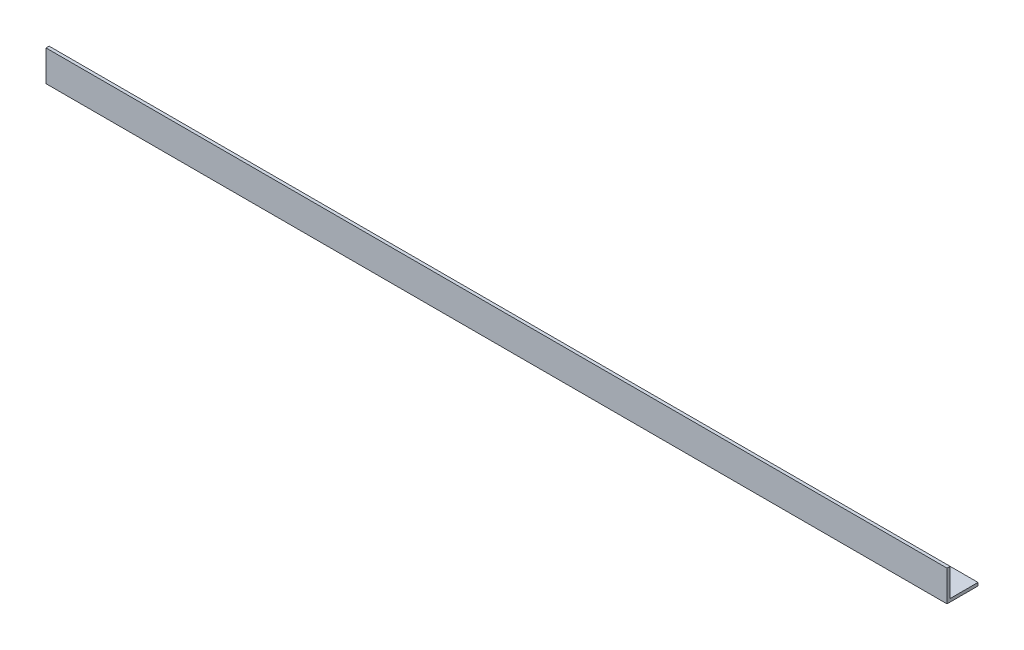
SolidWorks part; units mm, degrees
ref_plane "Спереди" through (0, 0, 0) normal (0, 0, 1) x (1, 0, 0)
ref_plane "Сверху" through (0, 0, 0) normal (0, 1, 0) x (1, 0, 0)
ref_plane "Справа" through (0, 0, 0) normal (1, 0, 0) x (0, 0, -1)
sketch "Эскиз1" plane through (0, 0, 0) normal (1, 0, 0) x (0, 0, -1)
  line L0 (0, 0) -> (0, 15)
  line L1 (0, 15) -> (1.5, 15)
  line L2 (1.5, 15) -> (1.5, 1.5)
  line L3 (1.5, 1.5) -> (15, 1.5)
  line L4 (15, 1.5) -> (15, 0)
  line L5 (15, 0) -> (0, 0)
  dimension "D1" = 15
  dimension "D2" = 15
  dimension "D3" = 1.5
  dimension "D4" = 1.5
extrude "Бобышка-Вытянуть1" add sketch "Эскиз1" along normal blind 436
